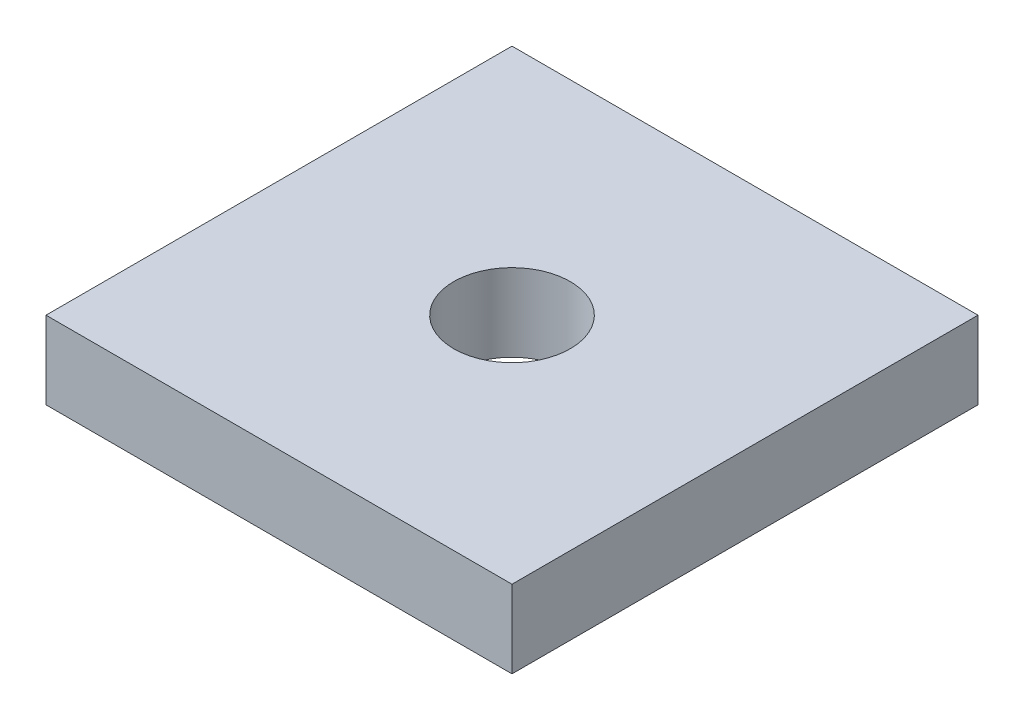
SolidWorks part; units mm, degrees
ref_plane "Front Plane" through (0, 0, 0) normal (0, 0, 1) x (1, 0, 0)
ref_plane "Top Plane" through (0, 0, 0) normal (0, 1, 0) x (1, 0, 0)
ref_plane "Right Plane" through (0, 0, 0) normal (1, 0, 0) x (0, 0, -1)
sketch "Sketch1" plane through (0, 0, 0) normal (0, 1, 0) x (1, 0, 0)
  line L1 (0, 0) -> (76.2, 0)
  line L2 (0, 0) -> (0, 76.2)
  line L3 (0, 76.2) -> (76.2, 76.2)
  line L4 (76.2, 0) -> (76.2, 76.2)
  circle A0 centre (38.1, 38.1) radius 9.525
  dimension "D5" = 19.05
  dimension "D1" = 76.2
  dimension "D2" = 76.2
  dimension "D3" = 38.1
  dimension "D4" = 38.1
extrude "Boss-Extrude1" add sketch "Sketch1" along normal blind 12.7
equation "\"D3@Sketch1\" = \"D1@Sketch1\"/2"
equation "\"D4@Sketch1\" = \"D2@Sketch1\"/2"
